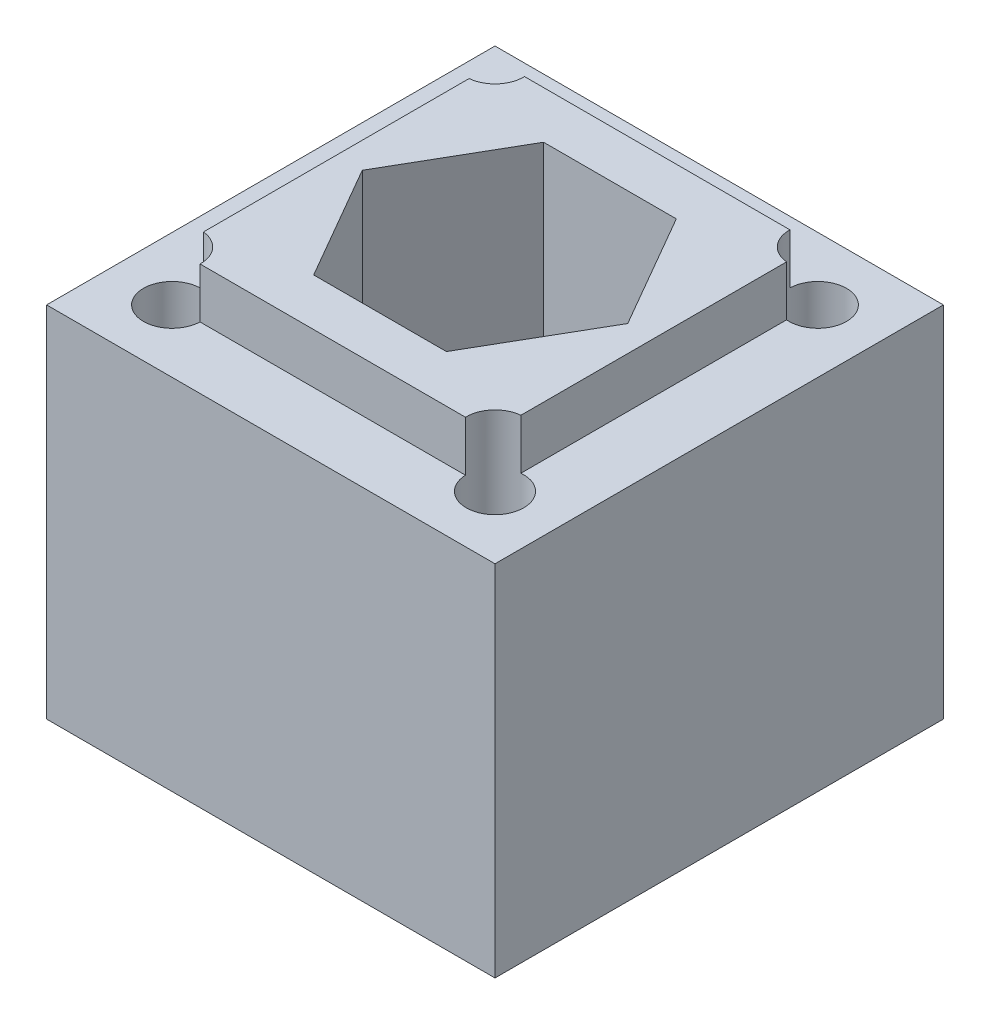
SolidWorks part; units mm, degrees
ref_plane "Спереди" through (0, 0, 0) normal (0, 0, 1) x (1, 0, 0)
ref_plane "Сверху" through (0, 0, 0) normal (0, 1, 0) x (1, 0, 0)
ref_plane "Справа" through (0, 0, 0) normal (1, 0, 0) x (0, 0, -1)
sketch "Sketch1" plane through (0, 0, 0) normal (0, 1, 0) x (1, 0, 0)
  line L1 (12.5, -12.5) -> (-12.5, -12.5)
  line L2 (12.5, -12.5) -> (12.5, 12.5)
  line L3 (12.5, 12.5) -> (-12.5, 12.5)
  line L4 (-12.5, -12.5) -> (-12.5, 12.5)
  line L5 (12.5, -12.5) -> (-12.5, 12.5) construction
  line L6 (12.5, 12.5) -> (-12.5, -12.5) construction
  point P0 (0, 0)
  dimension "D1" = 25
extrude "Boss-Extrude1" add sketch "Sketch1" along normal blind 20
sketch "Sketch4" plane through (0, 20, 0) normal (0, 1, 0) x (1, 0, 0)
  circle A0 centre (0, 0) radius 4.15
  dimension "D1" = 8.3
extrude "Cut-Extrude2" cut sketch "Sketch4" against normal through all
sketch "Sketch5" plane through (0, 20, 0) normal (0, 1, 0) x (1, 0, 0)
  line L1 (-3.7, -6.4086) -> (3.7, -6.4086)
  line L2 (3.7, -6.4086) -> (7.4, 0)
  line L3 (7.4, 0) -> (3.7, 6.4086)
  line L4 (3.7, 6.4086) -> (-3.7, 6.4086)
  line L5 (-3.7, 6.4086) -> (-7.4, 0)
  line L6 (-7.4, 0) -> (-3.7, -6.4086)
  line L7 (-12.5, -12.5) -> (12.5, -12.5) construction
  circle A0 centre (0, 0) radius 7.4 construction
  dimension "D1" = 14.8
extrude "Cut-Extrude3" cut sketch "Sketch5" against normal blind 7
sketch "Sketch9" plane through (0, 20, 0) normal (0, 1, 0) x (1, 0, 0)
  line L1 (8.85, 9.0463) -> (-8.85, 9.0463)
  line L2 (8.85, 9.0463) -> (8.85, -9.0463)
  line L3 (8.85, -9.0463) -> (-8.85, -9.0463)
  line L4 (-8.85, 9.0463) -> (-8.85, -9.0463)
  line L5 (8.85, 9.0463) -> (-8.85, -9.0463) construction
  line L6 (8.85, -9.0463) -> (-8.85, 9.0463) construction
  line L7 (-3.7, -6.4086) -> (3.7, -6.4086)
  line L8 (3.7, -6.4086) -> (7.4, 0)
  line L9 (7.4, 0) -> (3.7, 6.4086)
  line L10 (3.7, 6.4086) -> (-3.7, 6.4086)
  line L11 (-3.7, 6.4086) -> (-7.4, 0)
  line L12 (-7.4, 0) -> (-3.7, -6.4086)
  circle A0 centre (0, 0) radius 7.4 construction
  point P0 (0, 0)
  dimension "D2" = 14.8
  dimension "D1" = 17.7
extrude "Boss-Extrude3" add sketch "Sketch9" along normal blind 2.8
sketch "Sketch6" plane through (0, 20, 0) normal (0, 1, 0) x (1, 0, 0)
  line L1 (-9, 9) -> (9, 9) construction
  line L2 (-9, 9) -> (-9, -9) construction
  line L3 (-9, -9) -> (9, -9) construction
  line L4 (9, 9) -> (9, -9) construction
  line L5 (-9, 9) -> (9, -9) construction
  line L6 (-9, -9) -> (9, 9) construction
  circle A0 centre (9, -9) radius 1.6
  circle A1 centre (-9, -9) radius 1.6
  circle A2 centre (-9, 9) radius 1.6
  circle A3 centre (9, 9) radius 1.6
  point P0 (0, 0)
  dimension "D1" = 3.2
  dimension "D2" = 18
extrude "Cut-Extrude4" cut sketch "Sketch6" against normal through all both and the other way through all
